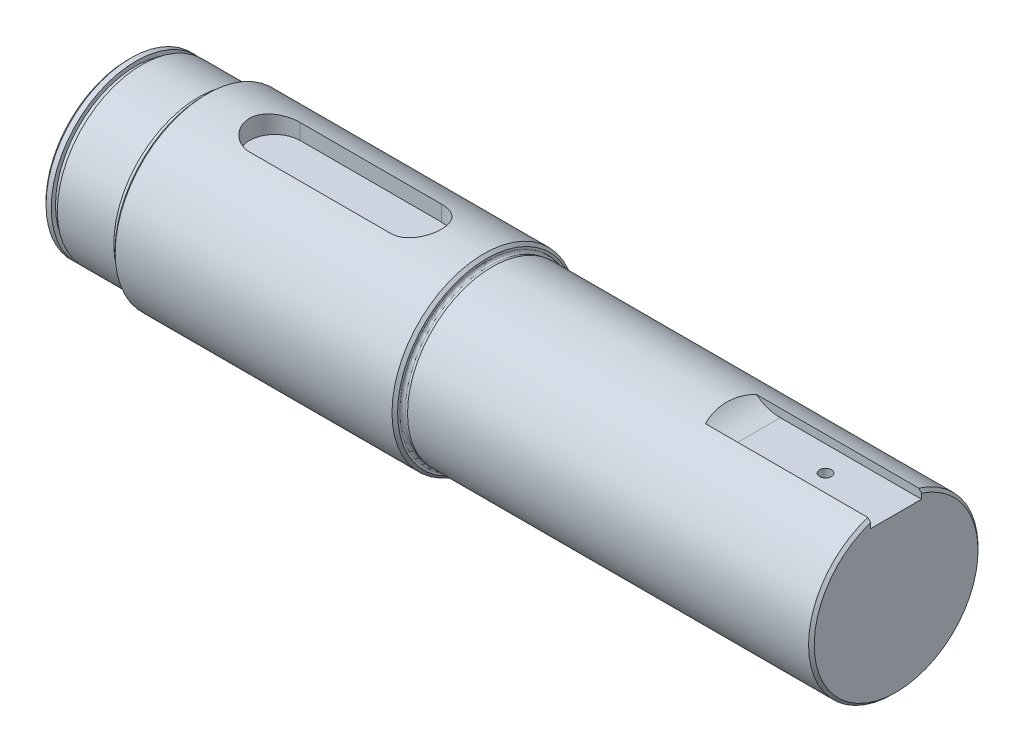
SolidWorks part; units mm, degrees
material "Plain Carbon Steel"
ref_plane "Front Plane" through (0, 0, 0) normal (0, 0, 1) x (1, 0, 0)
ref_plane "Top Plane" through (0, 0, 0) normal (0, 1, 0) x (1, 0, 0)
ref_plane "Right Plane" through (0, 0, 0) normal (1, 0, 0) x (0, 0, -1)
sketch "Sketch1" plane through (0, 0, 0) normal (0, 0, 1) x (1, 0, 0)
  line L0 (0, 0) -> (272, 0)
  line L1 (0, 0) -> (0, 30)
  line L2 (0, 30) -> (2.85, 30)
  line L4 (27, 32.5) -> (127, 32.5)
  line L5 (127, 32.5) -> (127, 30.7927)
  line L6 (129, 30) -> (272, 30)
  line L7 (272, 30) -> (272, 0)
  line L8 (2.85, 30) -> (2.85, 28.5)
  line L9 (2.85, 28.5) -> (5, 28.5)
  line L10 (5, 28.5) -> (5, 30)
  line L11 (5, 30) -> (25, 30)
  line L12 (127, 30.7927) -> (126.9751, 30.6998)
  line L13 (129, 30) -> (127.9549, 29.72)
  line L14 (126.9478, 31.2321) -> (126.9478, 30.3239) construction
  line L15 (127.0749, 29.6927) -> (129.1266, 29.6927) construction
  line L16 (77, 32.5) -> (77, -1.5864) construction
  line L17 (25, 30) -> (26.0451, 29.72)
  line L18 (27, 30.7927) -> (27.0249, 30.6998)
  line L19 (27, 30.7927) -> (27, 32.5)
  arc A0 (126.9751, 30.6998) -> (127.9549, 29.72) centre (127.7478, 30.4927) ccw
  arc A1 (27.0249, 30.6998) -> (26.0451, 29.72) centre (26.2522, 30.4927) cw
  point P22 (127.7478, 29.6927)
  point P23 (126.9478, 30.4927)
  dimension "D9" = 0.8
  dimension "D1" = 100
  dimension "D2" = 22
  dimension "D3" = 145
  dimension "D5" = 32.5
  dimension "D6" = 30
  dimension "D7" = 15
  dimension "D8" = 60
  dimension "D10" = 2
  dimension "D11" = 1.1
  dimension "D12" = 0.0522
  dimension "D13" = 0.3073
  dimension "D14" = 2.15
  dimension "D15" = 28.5
  dimension "D16" = 272
revolve "Revolve1" add sketch "Sketch1" angle 360 about L0
chamfer "Chamfer1" distance 1 angle 45 4 edges at (272, 0, 30) (0, 0, 30) (27, 0, 32.5) (127, 0, 32.5)
ref_plane "Plane1" through (0, 23.2, 0) normal (0, 1, 0) x (1, 0, 0)
ref_plane "Plane2" through (0, 25.7, 0) normal (0, 1, 0) x (1, 0, 0)
sketch "Sketch2" plane through (0, 25.7, 0) normal (0, 1, 0) x (1, 0, 0)
  line L0 (272, 9) -> (222, 9)
  line L1 (272, -29) -> (272, 29) construction
  line L2 (222, 9) -> (222, -9)
  line L3 (222, -9) -> (272, -9)
  line L4 (272, -9) -> (272, 0)
  line L5 (272, 0) -> (272, 9)
  line L6 (52, 0) -> (102, 0) construction
  line L7 (52, 9) -> (102, 9)
  line L8 (52, -9) -> (102, -9)
  line L9 (27, 31.5) -> (27, -31.5) construction
  arc A0 (52, 9) -> (52, -9) centre (52, 0) ccw
  arc A1 (102, -9) -> (102, 9) centre (102, 0) ccw
  point P10 (77, 0)
  dimension "D1" = 50
  dimension "D2" = 18
  dimension "D3" = 9
  dimension "D4" = 18
  dimension "D5" = 50
  dimension "D6" = 50
extrude "Cut-Extrude1" cut sketch "Sketch2" along normal up to next
sketch "Sketch3" plane through (0, 25.7, 0) normal (0, 1, 0) x (1, 0, 0)
  line L0 (222, -9) -> (222, 9) construction
  point P0 (247, 0)
  dimension "D1" = 25
hole_wizard "Ø5.0mm Dowel Hole1" positions "3DSketch1" profile "Sketch4" hole size "Ø5.0" standard "ISO"
sketch3d "3DSketch1"
  point P0 (247, 25.7, 0)
sketch "Sketch4" plane through (247, 25.7, 0) normal (1, 0, 0) x (0, 0, 1)
  line L0 (0, 0) -> (0, 6.2618)
  line L1 (0, 6.2618) -> (2.1, 5)
  line L2 (2.1, 5) -> (2.1, 0)
  line L5 (2.1, 0) -> (0, 0)
  line L10 (0, 6.2618) -> (-2.1, 5) construction
  line L11 (0, -6.35) -> (0, 107.95) construction
  dimension "Hole Dia." = 4.2
  dimension "Hole Depth" = 5
  dimension "Drill Angle" = 118
sketch "Sketch5" plane through (0, 0, 0) normal (0, 0, 1) x (1, 0, 0)
  line L0 (222, 30) -> (222, 25.7)
  line L1 (222, 28.6182) -> (222, 30) construction
  line L2 (35.75, 25.7) -> (-35.75, 25.7) construction
  line L3 (222, 28.6182) -> (222, 25.7) construction
  line L4 (222, 30) -> (212, 30)
  line L5 (222, 25.7) -> (226.6063, 25.7) construction
  arc A0 (222, 25.7) -> (212, 30) centre (222, 39.4779) cw
  dimension "D1" = 10
  dimension "D3" = 13.7779
  dimension "D2" = 4.3
extrude "Cut-Extrude2" cut sketch "Sketch5" against normal up to surface and the other way up to surface up to face at (251.9, 27.1359, -9) other way up to face at (251.7, 27.3459, 9)
